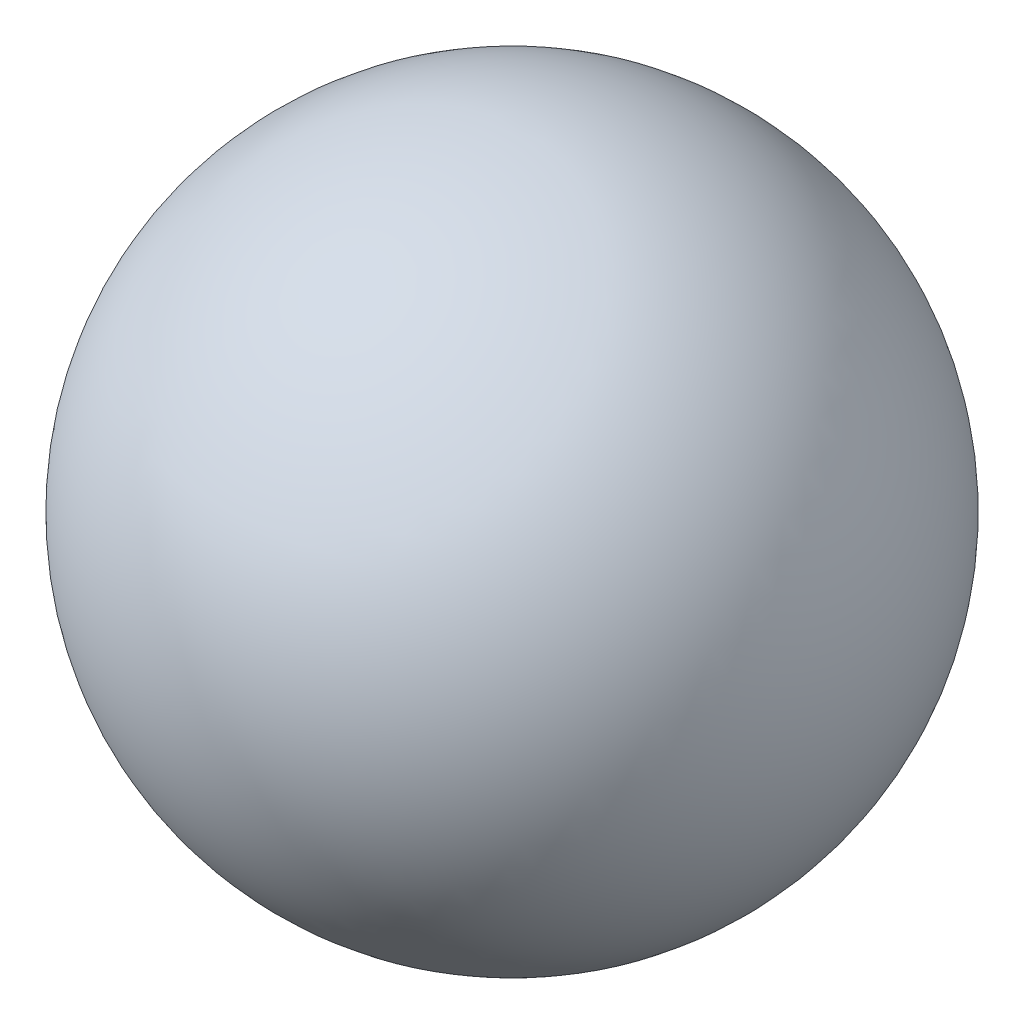
SolidWorks part; units mm, degrees
ref_plane "Front" through (0, 0, 0) normal (0, 0, 1) x (1, 0, 0)
ref_plane "Top" through (0, 0, 0) normal (0, 1, 0) x (1, 0, 0)
ref_plane "Right" through (0, 0, 0) normal (1, 0, 0) x (0, 0, -1)
sketch "Sketch1" plane through (0, 0, 0) normal (0, 0, 1) x (1, 0, 0)
  line L0 (-690.55, 787.4) -> (-690.55, 507.4) construction
  line L1 (-690.55, 937.4) -> (-690.55, 637.4) construction
  line L2 (-690.55, 937.4) -> (-690.55, 637.4)
  arc A0 (-690.55, 937.4) -> (-690.55, 637.4) centre (-690.55, 787.4) ccw
  circle A1 centre (-690.55, 787.4) radius 150 construction
revolve "Revolve1" add sketch "Sketch1" angle 360 about L1
sketch "Camera Point" plane through (0, 0, 0) normal (0, 0, 1) x (1, 0, 0)
  arc A0 (-690.55, 937.4) -> (-690.55, 637.4) centre (-690.55, 787.4) ccw construction
  point P0 (-840.55, 787.4)
equation "\"mass\"= \"human weight@FS2-FR-HA-A-0001-V1, HUMAN ANALOG.Assembly\" * \"head percent@FS2-FR-HA-A-0001-V1, HUMAN ANALOG.Assembly\" + \"helemet weight@FS2-FR-HA-A-0001-V1, HUMAN ANALOG.Assembly\""
